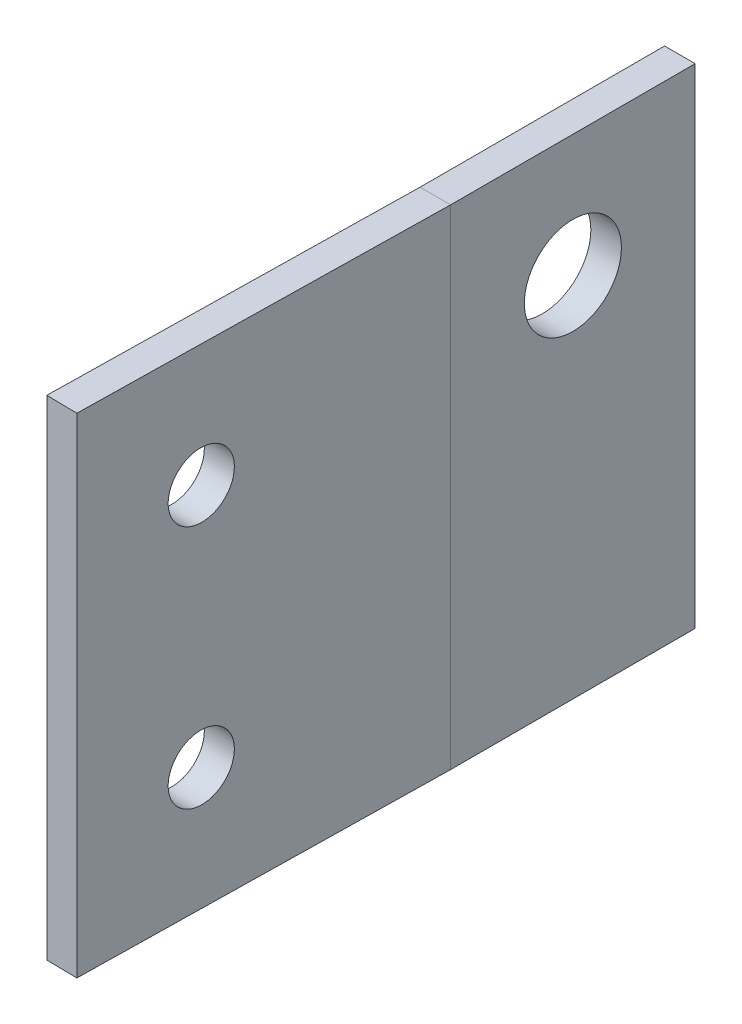
SolidWorks part; units mm, degrees
material "1060 Alloy"
ref_plane "Front Plane" through (0, 0, 0) normal (0, 0, 1) x (1, 0, 0)
ref_plane "Top Plane" through (0, 0, 0) normal (0, 1, 0) x (1, 0, 0)
ref_plane "Right Plane" through (0, 0, 0) normal (1, 0, 0) x (0, 0, -1)
sketch "Sketch1" plane through (0, 0, 0) normal (1, 0, 0) x (0, 0, -1)
  line L5 (12.7, -38.1) -> (-12.7, -38.1)
  line L6 (-12.7, -38.1) -> (-12.7, 12.7)
  line L7 (-12.7, 12.7) -> (12.7, 12.7)
  line L8 (12.7, 12.7) -> (12.7, -38.1)
  dimension "D1" = 50.8
  dimension "D2" = 12.7
  dimension "D3" = 12.7
  dimension "D4" = 12.7
extrude "Boss-Extrude1" add sketch "Sketch1" along normal blind 3.175 contours L7 L8 L5 L6
hole_wizard "3/8 Clearance Hole1" positions "Sketch2" profile "Sketch3" hole size "3/8" standard "ANSI Inch" end condition through all
sketch "Sketch2" plane through (3.175, 0, 0) normal (1, 0, 0) x (0, 0, -1)
  point P0 (0, 0)
sketch "Sketch3" plane through (3.175, 0, 0) normal (0, 1, 0) x (0, 0, -1)
  line L0 (0, 0) -> (0, 3.175)
  line L1 (0, 3.175) -> (5.0419, 3.175)
  line L2 (5.0419, 3.175) -> (5.0419, 0)
  line L5 (5.0419, 0) -> (0, 0)
  line L11 (0, -6.35) -> (0, 107.95) construction
  dimension "Thru Hole Dia." = 10.0838
  dimension "Thru Hole Depth" = 3.175
sketch "Sketch6" plane through (0, 12.7, 0) normal (0, 1, 0) x (1, 0, 0)
  line L0 (0, -12.7) -> (-0.6649, -50.7942)
  line L1 (-0.6649, -50.7942) -> (2.5096, -50.8496)
  line L2 (2.5096, -50.8496) -> (3.175, -12.7277)
  line L3 (3.175, -12.7277) -> (3.175, -12.7)
  line L4 (3.175, -12.7) -> (0, -12.7)
  line L5 (0, -12.7) -> (0, 12.7) construction
  line L6 (3.175, -12.7) -> (3.175, 12.7) construction
  dimension "D1" = 1
  dimension "D2" = 38.1
extrude "Boss-Extrude2" add sketch "Sketch6" against normal blind 50.8 separate body
hole_wizard "1/4 Clearance Hole1" positions "Sketch4" profile "Sketch5" hole size "1/4" standard "ANSI Inch" end condition through all
sketch "Sketch4" plane through (2.9604, 0, 25.0227) normal (-0.9998, 0, -0.0175) x (-0.0175, 0, 0.9998)
  line L1 (13.1308, 0) -> (13.1308, -25.4) construction
  line L5 (25.8308, -38.1) -> (25.8308, 12.7) construction
  line L7 (25.8308, 12.7) -> (-12.2969, 12.7) construction
  point P0 (13.1308, 0)
  point P4 (13.1308, -25.4)
  dimension "D1" = 12.7
  dimension "D2" = 25.4
  dimension "D3" = 12.7
sketch "Sketch5" plane through (2.7312, 0, 38.1515) normal (0, 1, 0) x (0.0175, 0, -0.9998)
  line L0 (0, 0) -> (0, 3.8398)
  line L1 (0, 3.8398) -> (3.3782, 3.8398)
  line L2 (3.3782, 3.8398) -> (3.3782, 0)
  line L5 (3.3782, 0) -> (0, 0)
  line L11 (0, -6.35) -> (0, 107.95) construction
  dimension "Thru Hole Dia." = 6.7564
  dimension "Thru Hole Depth" = 3.8398
